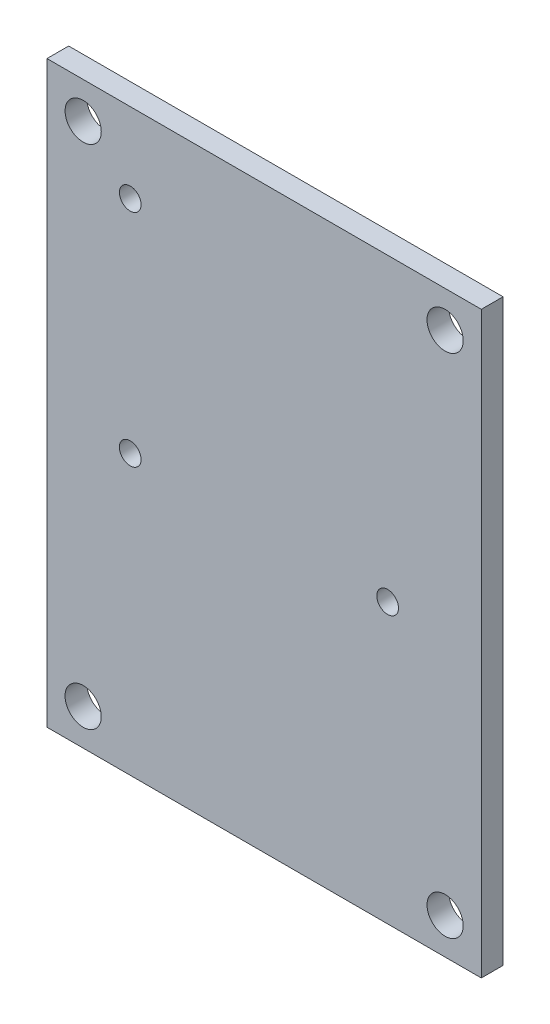
SolidWorks part; units mm, degrees
material "Custom Plastic"
ref_plane "Front Plane" through (0, 0, 0) normal (0, 0, 1) x (1, 0, 0)
ref_plane "Top Plane" through (0, 0, 0) normal (0, 1, 0) x (1, 0, 0)
ref_plane "Right Plane" through (0, 0, 0) normal (1, 0, 0) x (0, 0, -1)
sketch "Sketch1" plane through (0, 0, 0) normal (0, 0, 1) x (1, 0, 0)
  line L1 (-30, 40) -> (30, 40)
  line L2 (-30, 40) -> (-30, -40)
  line L3 (-30, -40) -> (30, -40)
  line L4 (30, 40) -> (30, -40)
  line L5 (-30, 40) -> (30, -40) construction
  line L6 (-30, -40) -> (30, 40) construction
  point P0 (0, 0)
  dimension "D1" = 60
  dimension "D2" = 80
extrude "Boss-Extrude1" add sketch "Sketch1" against normal blind 3
sketch "Sketch2" plane through (0, 0, 0) normal (0, 0, 1) x (1, 0, 0)
  line L0 (0, 0) -> (0, 40) construction
  line L1 (30, 40) -> (-30, 40) construction
  line L2 (0, 40) -> (-30, 40) construction
  line L3 (-30, 40) -> (-30, 0) construction
  line L4 (-30, 40) -> (-30, -40) construction
  line L5 (-30, 0) -> (0, 0) construction
  circle A0 centre (-25, 35) radius 2.5
  circle A1 centre (-25, -35) radius 2.5
  circle A2 centre (25, -35) radius 2.5
  circle A3 centre (25, 35) radius 2.5
  dimension "D2" = 5
  dimension "D1" = 5
  dimension "D3" = 5
extrude "Cut-Extrude1" cut sketch "Sketch2" against normal blind 3
sketch "Sketch3" plane through (0, 0, 0) normal (0, 0, 1) x (1, 0, 0)
  line L0 (-30, 40) -> (-30, -40) construction
  line L1 (30, 40) -> (-30, 40) construction
  circle A0 centre (-18.5, 29) radius 1.5
  circle A1 centre (-18.5, -1.48) radius 1.5
  circle A2 centre (17.06, -1.48) radius 1.5
  dimension "D5" = 3
  dimension "D6" = 3
  dimension "D7" = 3
  dimension "D2" = 11.5
  dimension "D3" = 11.5
  dimension "D4" = 11
  dimension "D10" = 30.48
  dimension "D12" = 35.56
  dimension "D13" = 30.48
extrude "Cut-Extrude2" cut sketch "Sketch3" against normal blind 3
